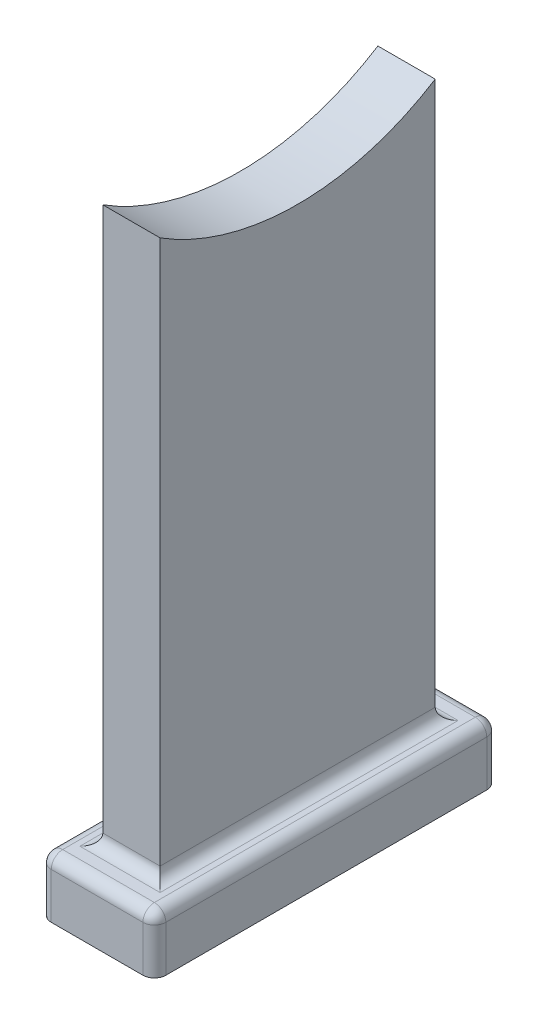
SolidWorks part; units mm, degrees
ref_plane "정면" through (0, 0, 0) normal (0, 0, 1) x (1, 0, 0)
ref_plane "윗면" through (0, 0, 0) normal (0, 1, 0) x (1, 0, 0)
ref_plane "우측면" through (0, 0, 0) normal (1, 0, 0) x (0, 0, -1)
sketch "스케치1" plane through (0, 0, 0) normal (0, 1, 0) x (1, 0, 0)
  line L0 (-123.9164, 0) -> (140.3655, 0) construction
  line L1 (0, 75.2742) -> (0, -78.564) construction
  line L3 (10, -30) -> (-10, -30)
  line L4 (10, -30) -> (10, 30)
  line L5 (10, 30) -> (-10, 30)
  line L6 (-10, -30) -> (-10, 30)
  line L7 (10, -30) -> (-10, 30) construction
  line L8 (10, 30) -> (-10, -30) construction
  point P5 (0, 0)
  dimension "D1" = 60
  dimension "D2" = 20
extrude "보스-돌출1" add sketch "스케치1" along normal blind 10
sketch "스케치5" plane through (0, 0, 0) normal (1, 0, 0) x (0, 0, -1)
  line L0 (-144.0437, 0) -> (208.6112, 0) construction
  line L1 (0, -164.5736) -> (0, 216.7048) construction
  line L2 (-30, 10) -> (-30, 0) construction
  line L3 (-24, 0) -> (24, 0)
  line L4 (-24, 0) -> (-24, 100)
  line L6 (24, 0) -> (24, 100)
  line L7 (30, 10) -> (30, 0) construction
  line L8 (24, 100) -> (24, 106.9343)
  line L10 (-24, 106.9343) -> (-24, 100)
  arc A0 (-24, 106.9343) -> (24, 106.9343) centre (0, 145) ccw
  dimension "D4" = 90
  dimension "D1" = 100
  dimension "D2" = 6
  dimension "D3" = 6
extrude "보스-돌출3" add sketch "스케치5" along normal mid plane 10
fillet "필렛1" radius 2 12 edges at (0, 10, -24) (-5, 10, 0) (0, 10, 24) (5, 10, 0) (0, 10, -30) (-10, 10, 0) (0, 10, 30) (10, 10, 0) (-10, 5, -30) (10, 5, -30) (10, 5, 30) (-10, 5, 30)
